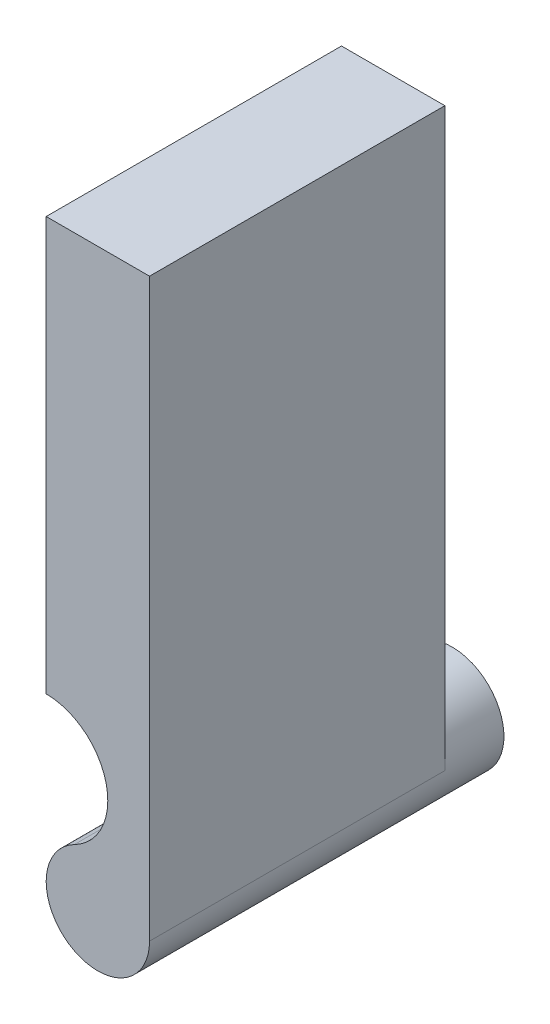
SolidWorks part; units mm, degrees
ref_plane "Front Plane" through (0, 0, 0) normal (0, 0, 1) x (1, 0, 0)
ref_plane "Top Plane" through (0, 0, 0) normal (0, 1, 0) x (1, 0, 0)
ref_plane "Right Plane" through (0, 0, 0) normal (1, 0, 0) x (0, 0, -1)
sketch "Szkic1" plane through (0, 0, 0) normal (0, 0, 1) x (1, 0, 0)
  line L0 (1.75, 0) -> (1.75, 19.5)
  line L1 (-1.75, 19.5) -> (-1.75, 5.5)
  line L2 (-1.75, 19.5) -> (1.75, 19.5)
  arc A0 (-0.7983, 1.5573) -> (1.75, 0) centre (0, 0) ccw
  arc A1 (-1.75, 5.5) -> (-0.7983, 1.5573) centre (-1.75, 3.4138) cw
  dimension "D1" = 3.5
  dimension "D2" = 14
  dimension "D3" = 3.5
  dimension "D4" = 19.5
extrude "Dodanie-wyciągnięcie1" add sketch "Szkic1" along normal blind 10
sketch "Szkic2" plane through (0, 0, 0) normal (0, 0, -1) x (-1, 0, 0)
  circle A0 centre (0, 0) radius 1.75
  arc A1 (-1.75, 0) -> (0.7983, 1.5573) centre (0, 0) ccw construction
extrude "Dodanie-wyciągnięcie2" add sketch "Szkic2" along normal blind 2
